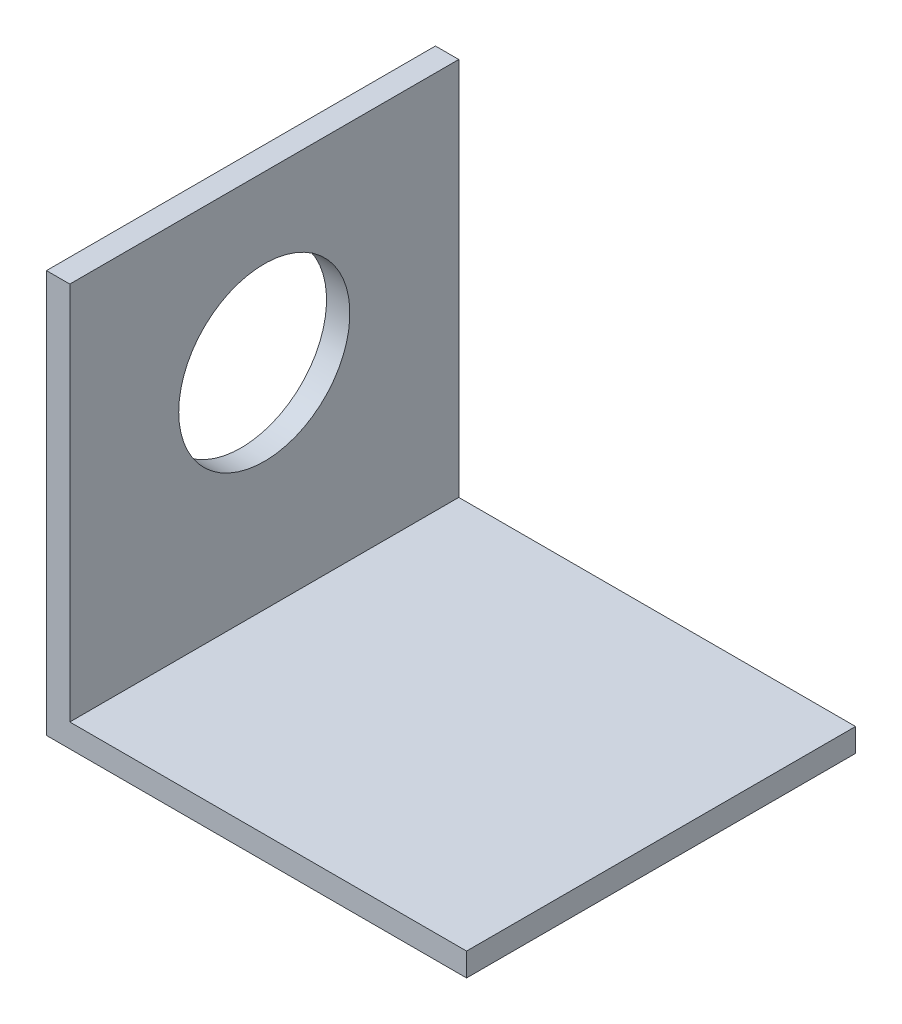
SolidWorks part; units mm, degrees
ref_plane "Front Plane" through (0, 0, 0) normal (0, 0, 1) x (1, 0, 0)
ref_plane "Top Plane" through (0, 0, 0) normal (0, 1, 0) x (1, 0, 0)
ref_plane "Right Plane" through (0, 0, 0) normal (1, 0, 0) x (0, 0, -1)
sketch "Sketch1" plane through (0, 0, 0) normal (0, 1, 0) x (1, 0, 0)
  line L1 (-27, 25) -> (27, 25)
  line L2 (-27, 25) -> (-27, -25)
  line L3 (-27, -25) -> (27, -25)
  line L4 (27, 25) -> (27, -25)
  line L5 (-27, 25) -> (27, -25) construction
  line L6 (-27, -25) -> (27, 25) construction
  point P0 (0, 0)
  dimension "D1" = 50
  dimension "D2" = 54
extrude "Boss-Extrude1" add sketch "Sketch1" along normal blind 3
sketch "Sketch2" plane through (0, 3, 0) normal (0, 1, 0) x (1, 0, 0)
  line L0 (-27, -25) -> (27, -25) construction
  line L1 (-27, 25) -> (-24, 25)
  line L2 (-27, 25) -> (-27, -25)
  line L3 (-27, -25) -> (-24, -25)
  line L4 (-24, 25) -> (-24, -25)
  dimension "D1" = 3
extrude "Boss-Extrude2" add sketch "Sketch2" along normal blind 48.75
sketch "Sketch3" plane through (-27, 0, 0) normal (-1, 0, 0) x (0, 0, 1)
  line L0 (0, 51.75) -> (0, 0) construction
  line L1 (-25, 51.75) -> (25, 51.75) construction
  circle A0 centre (0, 30.5) radius 11
  dimension "D1" = 22
  dimension "D2" = 21.25
extrude "Cut-Extrude1" cut sketch "Sketch3" against normal through all
